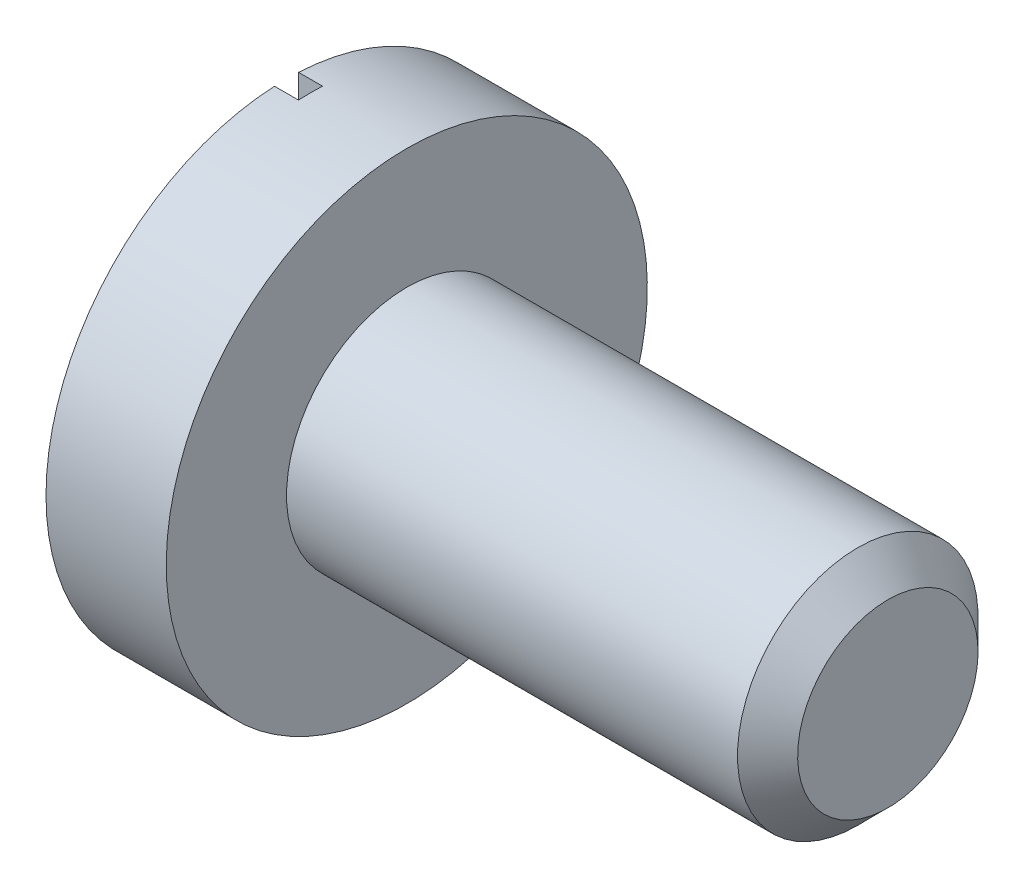
SolidWorks part; units mm, degrees
ref_plane "Front Plane" through (0, 0, 0) normal (0, 0, 1) x (1, 0, 0)
ref_plane "Top Plane" through (0, 0, 0) normal (0, 1, 0) x (1, 0, 0)
ref_plane "Right Plane" through (0, 0, 0) normal (1, 0, 0) x (0, 0, -1)
sketch "Croquis1" plane through (0, 0, 0) normal (0, 0, 1) x (1, 0, 0)
  line L0 (0, 0) -> (0, 1)
  line L1 (0, 1) -> (0.5, 1)
  line L2 (0.5, 1) -> (0.5, 0.5)
  line L3 (0.5, 0.5) -> (2.5, 0.5)
  line L6 (2.5, 0.5) -> (2.5, 0)
  line L7 (2.5, 0) -> (0, 0)
  dimension "D1" = 1
  dimension "D2" = 0.5
  dimension "D3" = 2.5
  dimension "D5" = 0.5
revolve "Revolución1" add sketch "Croquis1" angle 360 about L7
cosmetic thread "Rosca cosmética1" parameters "D2"=0.75
chamfer "Chaflán1" distance 0.125 angle 45 1 edges at (2.5, 0.5, 0)
sketch "Croquis5" plane through (0, 0, 0) normal (-1, 0, 0) x (0, 0, 1)
  line L2 (-0.05, 0.9987) -> (-0.05, -0.9987)
  line L4 (0.05, 0.9987) -> (0.05, -0.9987)
  circle A0 centre (0, 0) radius 1 construction
  arc A1 (-0.05, -0.9987) -> (0.05, -0.9987) centre (0, 0) ccw
  arc A2 (0.05, 0.9987) -> (-0.05, 0.9987) centre (0, 0) ccw
  point P3 (0.05, 0)
  point P4 (0, 1)
  dimension "D1" = 0.1
extrude "Cortar-Extruir1" cut sketch "Croquis5" against normal blind 0.1
